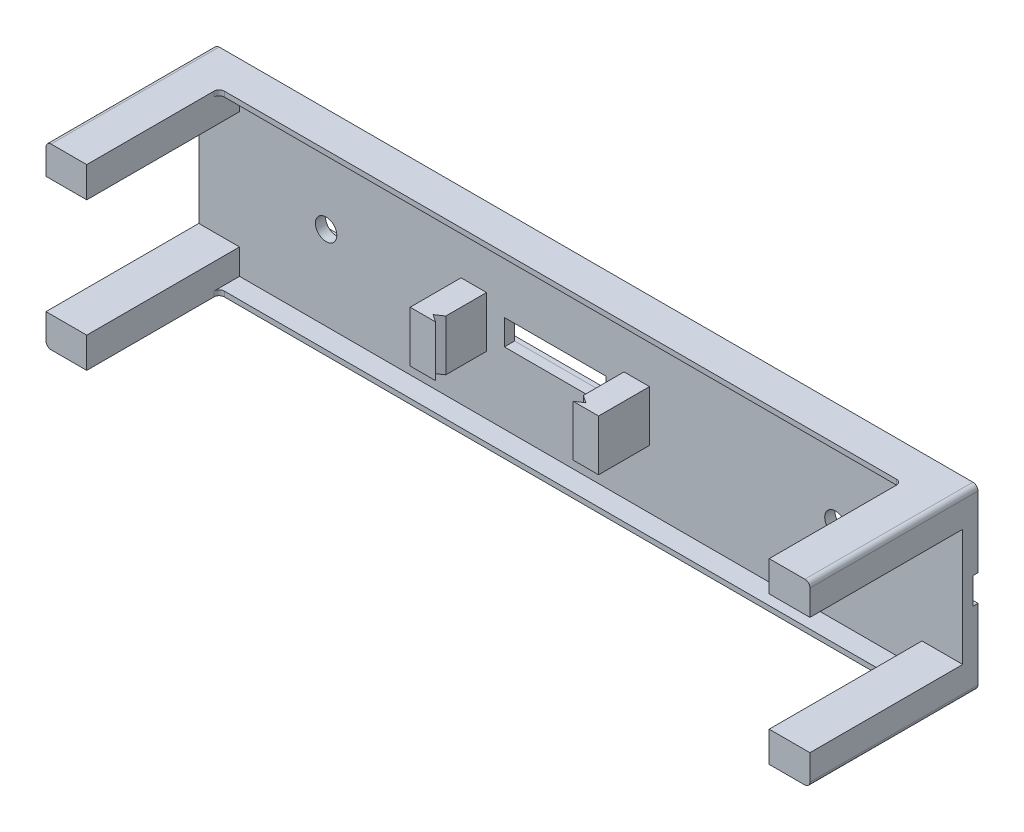
SolidWorks part; units mm, degrees
ref_plane "Přední rovina" through (0, 0, 0) normal (0, 0, 1) x (1, 0, 0)
ref_plane "Horní rovina" through (0, 0, 0) normal (0, 1, 0) x (1, 0, 0)
ref_plane "Pravá rovina" through (0, 0, 0) normal (1, 0, 0) x (0, 0, -1)
sketch "Skica1" plane through (0, 0, 0) normal (0, 0, 1) x (1, 0, 0)
  line L1 (75, 17.5) -> (-75, 17.5)
  line L2 (75, 17.5) -> (75, -17.5)
  line L3 (75, -17.5) -> (-75, -17.5)
  line L4 (-75, 17.5) -> (-75, -17.5)
  line L5 (75, 17.5) -> (-75, -17.5) construction
  line L6 (75, -17.5) -> (-75, 17.5) construction
  point P0 (0, 0)
  point P5 (-27.5, 0)
  point P11 (4.5, 0)
  dimension "D1" = 35
  dimension "D2" = 150
extrude "Přidat vysunutím2" add sketch "Skica1" along normal blind 3 contours L2 L1 L4 L3
sketch "Skica4" plane through (0, 0, 3) normal (0, 0, 1) x (1, 0, 0)
  line L0 (-19.25, -5.75) -> (-19.25, 5.75) construction
  line L1 (-15, 2.5) -> (5, 2.5)
  line L2 (-15, 2.5) -> (-15, -2.5)
  line L3 (-15, -2.5) -> (5, -2.5)
  line L4 (5, 2.5) -> (5, -2.5)
  line L5 (-15, 2.5) -> (5, -2.5) construction
  line L6 (-15, -2.5) -> (5, 2.5) construction
  line L7 (9.25, 5.75) -> (9.25, -5.75) construction
  point P0 (-5, 0)
  point P7 (-19.25, 0)
  dimension "D1" = 5
  dimension "D2" = 20
  dimension "D3" = 4.25
  dimension "D4" = 4.25
extrude "Odebrat vysunutím1" cut sketch "Skica4" against normal blind 2
sketch "Skica5" plane through (0, 0, 0) normal (0, 0, -1) x (-1, 0, 0)
  line L10 (75, 17.5) -> (75, -17.5) construction
  line L11 (-75, 2.6) -> (75, 2.6)
  line L12 (-75, 2.6) -> (-75, -2.6)
  line L13 (-75, -2.6) -> (75, -2.6)
  line L14 (75, 2.6) -> (75, -2.6)
  line L15 (-75, 2.6) -> (75, -2.6) construction
  line L16 (-75, -2.6) -> (75, 2.6) construction
  point P0 (0, 0)
  dimension "D1" = 5.2
extrude "Odebrat vysunutím3" cut sketch "Skica5" against normal blind 1 contours L11 L14 L13 L12
sketch "Skica7" plane through (0, 0, 1) normal (0, 0, -1) x (-1, 0, 0)
  circle A0 centre (-50, 0) radius 2.1
  circle A1 centre (50, 0) radius 2.1
  dimension "D1" = 4.2
  dimension "D2" = 50
  dimension "D3" = 50
extrude "Odebrat vysunutím4" cut sketch "Skica7" against normal through all
sketch "Skica8" plane through (0, 0, 3) normal (0, 0, 1) x (1, 0, 0)
  line L0 (0, 0) -> (0, -17.5) construction
  line L1 (75, 17.5) -> (67, 17.5)
  line L2 (75, 17.5) -> (75, 11.5)
  line L3 (75, 11.5) -> (67, 11.5)
  line L4 (67, 17.5) -> (67, 11.5)
  line L5 (75, -17.5) -> (67, -17.5)
  line L6 (75, -17.5) -> (75, -11.5)
  line L7 (75, -11.5) -> (67, -11.5)
  line L8 (67, -17.5) -> (67, -11.5)
  line L9 (75, -17.5) -> (-75, -17.5) construction
  line L10 (-67, -17.5) -> (-67, -11.5)
  line L11 (-75, -17.5) -> (-67, -17.5)
  line L12 (-75, -17.5) -> (-75, -11.5)
  line L13 (-75, -11.5) -> (-67, -11.5)
  line L14 (-75, 17.5) -> (-75, 11.5)
  line L15 (-75, 17.5) -> (-67, 17.5)
  line L16 (-67, 17.5) -> (-67, 11.5)
  line L17 (-75, 11.5) -> (-67, 11.5)
  dimension "D1" = 6
  dimension "D2" = 8
extrude "Přidat vysunutím4" add sketch "Skica8" along normal blind 30
fillet "Zaoblit1" radius 1 4 edges at (75, 17.5, 16.5) (75, -17.5, 16.5) (-75, 17.5, 16.5) (-75, -17.5, 16.5)
sketch "Skica9" plane through (0, 0, 3) normal (0, 0, 1) x (1, 0, 0)
  line L0 (-67, 11.5) -> (-67, 17.5) construction
  line L1 (67, 17.5) -> (-67, 17.5)
  line L2 (67, 17.5) -> (67, 16.5)
  line L3 (67, 16.5) -> (-67, 16.5)
  line L4 (-67, 17.5) -> (-67, 16.5)
  line L5 (67, -11.5) -> (67, -17.5) construction
  line L6 (-67, -17.5) -> (67, -17.5)
  line L7 (-67, -17.5) -> (-67, -16.5)
  line L8 (-67, -16.5) -> (67, -16.5)
  line L9 (67, -17.5) -> (67, -16.5)
  dimension "D1" = 1
  dimension "D2" = 1
extrude "Přidat vysunutím5" add sketch "Skica9" along normal blind 4
fillet "Zaoblit2" radius 1 4 edges at (-67, -17, 7) (67, -17, 7) (67, 17, 7) (-67, 17, 7)
sketch "Skica10" plane through (0, 0, 3) normal (0, 0, 1) x (1, 0, 0)
  line L5 (-15, 2.5) -> (-15, -2.5) construction
  line L6 (-18.5, 5) -> (-23.5, 5)
  line L7 (8.5, 5) -> (13.5, 5)
  line L8 (8.5, 5) -> (8.5, -5)
  line L9 (8.5, -5) -> (13.5, -5)
  line L10 (13.5, 5) -> (13.5, -5)
  line L11 (8.5, 5) -> (13.5, -5) construction
  line L12 (8.5, -5) -> (13.5, 5) construction
  line L14 (-18.5, 5) -> (-18.5, -5)
  line L15 (-18.5, -5) -> (-23.5, -5)
  line L16 (-23.5, 5) -> (-23.5, -5)
  line L17 (-18.5, 5) -> (-23.5, -5) construction
  line L18 (-18.5, -5) -> (-23.5, 5) construction
  line L19 (5, -2.5) -> (5, 2.5) construction
  point P0 (-21, 0)
  point P5 (11, 0)
  point P10 (-18.5, 0)
  dimension "D1" = 10
  dimension "D2" = 5
  dimension "D3" = 5
  dimension "D4" = 27
  dimension "D5" = 10
  dimension "D6" = 3.5
  dimension "D7" = 3.5
  dimension "D8" = 0
extrude "Přidat vysunutím6" add sketch "Skica10" along normal blind 10
sketch "Skica12" plane through (0, 5, 0) normal (0, 1, 0) x (1, 0, 0)
  line L0 (-18.5, -13) -> (-18.5, -11)
  line L1 (-18.5, -13) -> (-18.5, -3) construction
  line L2 (-18.5, -11) -> (-20, -12)
  line L3 (-20, -12) -> (-18.5, -13)
  line L4 (8.5, -13) -> (8.5, -11)
  line L5 (8.5, -13) -> (8.5, -3) construction
  line L6 (8.5, -11) -> (10, -12)
  line L7 (10, -12) -> (8.5, -13)
  dimension "D2" = 1.5
  dimension "D1" = 2
  dimension "D3" = 1.5
extrude "Odebrat vysunutím6" cut sketch "Skica12" against normal blind 10
